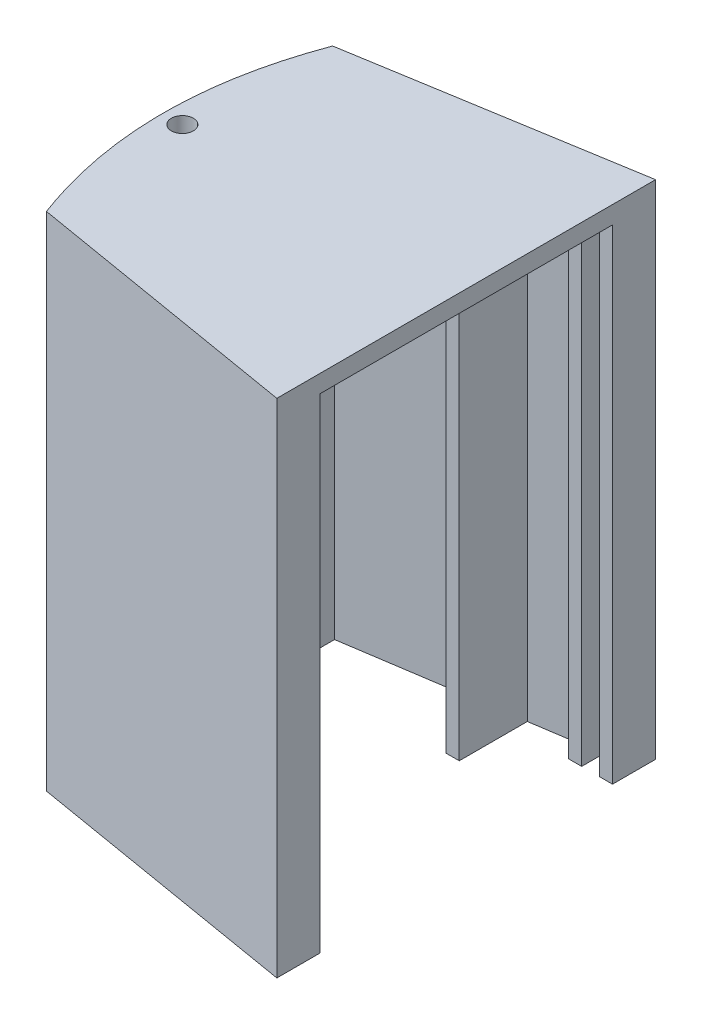
SolidWorks part; units mm, degrees
ref_plane "Alzado" through (0, 0, 0) normal (0, 0, 1) x (1, 0, 0)
ref_plane "Planta" through (0, 0, 0) normal (0, 1, 0) x (1, 0, 0)
ref_plane "Vista lateral" through (0, 0, 0) normal (1, 0, 0) x (0, 0, -1)
sketch "Croquis1" plane through (0, 0, 0) normal (0, 1, 0) x (1, 0, 0)
  line L0 (27.2041, 42.8965) -> (27.2041, 39.1152)
  line L1 (-32.7959, 30) -> (2.2041, 35.3172)
  line L2 (-32.7959, -30) -> (2.2041, -35.4284)
  line L3 (27.2041, -39.3059) -> (27.2041, -43.1035)
  line L4 (-32.7959, 30) -> (-32.7959, -30)
  line L5 (-35.7454, 32.5135) -> (27.2041, 42.8965)
  line L6 (-35.7102, -32.5093) -> (27.2041, -43.1035)
  line L7 (5.2041, 35.773) -> (17.2041, 37.596)
  line L8 (5.2041, 20.3172) -> (5.2041, 35.773)
  line L9 (5.2041, -20.4284) -> (5.2041, -35.8937)
  line L10 (2.2041, 20.3172) -> (2.2041, 35.3172)
  line L11 (2.2041, -20.4284) -> (2.2041, -35.4284)
  line L12 (5.2041, -35.8937) -> (17.2041, -37.7549)
  line L13 (27.2041, 39.1152) -> (27.2041, 33.1152)
  line L14 (27.2041, -39.3059) -> (27.2041, -33.3059)
  line L15 (17.2041, -33.3059) -> (20.2041, -33.3059)
  line L16 (5.2041, 20.3172) -> (2.2041, 20.3172)
  line L17 (5.2041, -20.4284) -> (2.2041, -20.4284)
  line L18 (17.2041, 33.1152) -> (20.2041, 33.1152)
  line L19 (17.2041, 33.1152) -> (17.2041, 37.596)
  line L20 (17.2041, -33.3059) -> (17.2041, -37.7549)
  line L21 (27.2041, 33.1152) -> (24.2041, 33.1152)
  line L22 (20.2041, 33.1152) -> (20.2041, 38.0517)
  line L23 (24.2041, 33.1152) -> (24.2041, 38.6594)
  line L24 (20.2041, 38.0517) -> (24.2041, 38.6594)
  line L25 (27.2041, -33.3059) -> (24.2041, -33.3059)
  line L26 (20.2041, -33.3059) -> (20.2041, -38.2202)
  line L27 (24.2041, -33.3059) -> (24.2041, -38.8406)
  line L28 (20.2041, -38.2202) -> (24.2041, -38.8406)
  spline S1 degree 2 poles (-35.7454, 32.5135) (-47.8641, -0.0044) (-35.7102, -32.5093) knots 0 0 0 1 1 1
  point P0 (0, 0)
  dimension "D1" = 63.8
  dimension "D2" = 63.8
extrude "Saliente-Extruir11" add sketch "Croquis1" along normal blind 110
sketch "Croquis6" plane through (0, 110, 0) normal (0, 1, 0) x (1, 0, 0)
  line L0 (-35.7454, 32.5135) -> (27.2041, 42.8965)
  line L1 (27.2041, 42.8965) -> (27.2041, -43.1035)
  line L2 (27.2041, -43.1035) -> (-35.7102, -32.5093)
  spline S0 degree 2 poles (-35.7454, 32.5135) (-47.8641, -0.0044) (-35.7102, -32.5093) knots 0 0 0 1 1 1
extrude "Saliente-Extruir12" add sketch "Croquis6" along normal blind 4
sketch "Croquis7" plane through (0, 0, 0) normal (0, -1, 0) x (1, 0, 0)
  circle A0 centre (-37.3568, 0) radius 2.5
  dimension "D1" = 5
extrude "Cortar-Extruir2" cut sketch "Croquis7" against normal through all both and the other way through all
